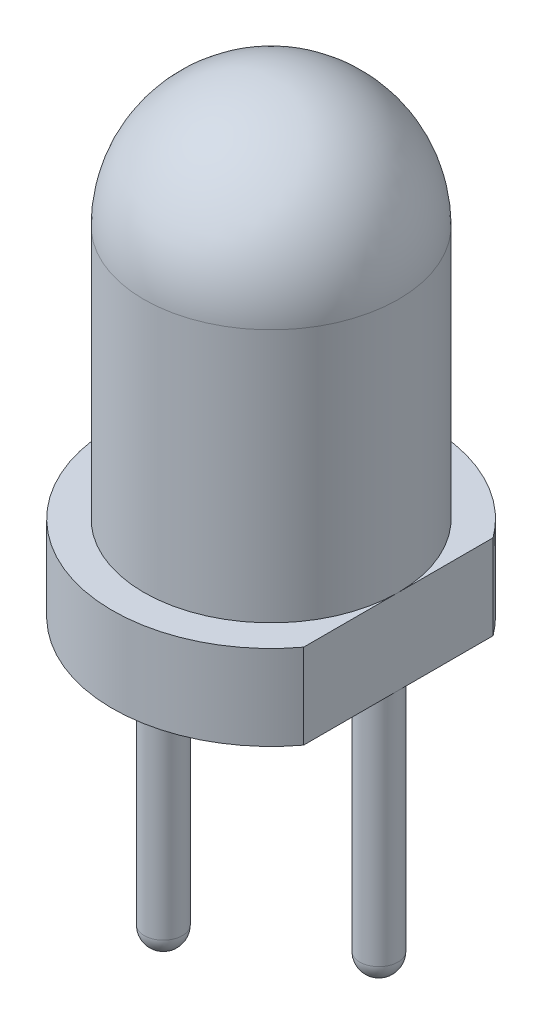
SolidWorks part; units mm, degrees
ref_plane "Front Plane" through (0, 0, 0) normal (0, 0, 1) x (1, 0, 0)
ref_plane "Top Plane" through (0, 0, 0) normal (0, 1, 0) x (1, 0, 0)
ref_plane "Right Plane" through (0, 0, 0) normal (1, 0, 0) x (0, 0, -1)
sketch "Sketch2" plane through (0, 0, 0) normal (0, 0, 1) x (1, 0, 0)
  line L0 (0, 0) -> (0, 6.8182) construction
  line L1 (0, 0) -> (-1.87, 0)
  line L2 (-1.87, 0) -> (-1.87, 1)
  line L3 (-1.87, 1) -> (-1.5, 1)
  line L4 (-1.5, 1) -> (-1.5, 3.99)
  line L5 (0, 0) -> (0, 5.49)
  arc A0 (-1.5, 3.99) -> (0, 5.49) centre (0, 3.99) cw
  dimension "D4" = 1.5
  dimension "D1" = 1
  dimension "D2" = 1.87
  dimension "D3" = 1.5
  dimension "D5" = 5.49
revolve "Revolve1" add sketch "Sketch2" angle 360 about L0
sketch "Sketch3" plane through (0, 0, 0) normal (0, -1, 0) x (1, 0, 0)
  line L0 (1.5, 1.1166) -> (1.5, -1.1166)
  circle A0 centre (0, 0) radius 1.87
  circle M2 centre (0, 0) radius 1.87
  dimension "D1" = 3.74
  dimension "D2" = 1.5
extrude "Cortar-Extruir1" cut sketch "Sketch3" against normal up to next contours L0 M2
sketch "Croquis1" plane through (0, 0, 0) normal (0, -1, 0) x (1, 0, 0)
  circle A0 centre (0, 0) radius 1.27 construction
  circle A1 centre (1.27, 0) radius 0.225
  circle A2 centre (-1.27, 0) radius 0.225
  dimension "D1" = 2.54
  dimension "D2" = 0.45
  dimension "D3" = 0.45
extrude "Saliente-Extruir1" add sketch "Croquis1" along normal blind 4
sketch "Croquis2" plane through (0, -4, 0) normal (0, -1, 0) x (1, 0, 0)
  circle A1 centre (1.27, 0) radius 0.225
  circle A2 centre (1.27, 0) radius 0.225
  dimension "D1" = 0
extrude "Cortar-Extruir2" cut sketch "Croquis2" against normal blind 1 contours A2
fillet "Redondeo1" radius 0.225 2 edges at (1.27, -3, -0.225) (-1.27, -4, -0.225)
